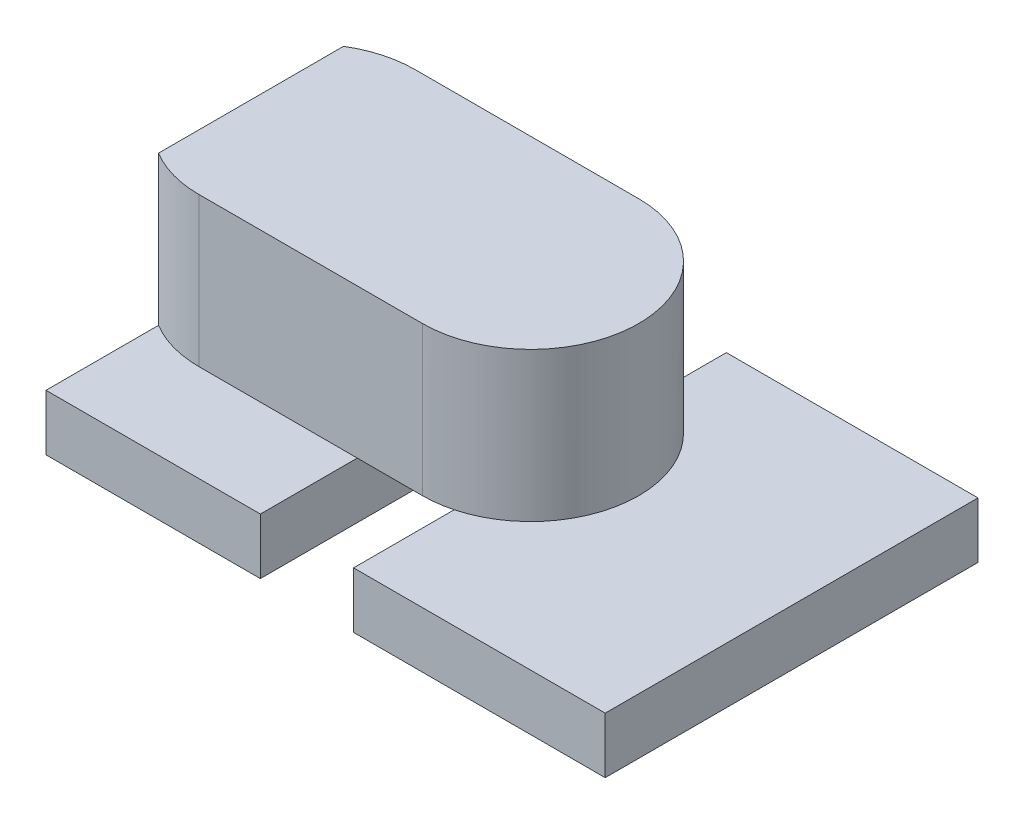
SolidWorks part; units mm, degrees
ref_plane "Front Plane" through (0, 0, 0) normal (0, 0, 1) x (1, 0, 0)
ref_plane "Top Plane" through (0, 0, 0) normal (0, 1, 0) x (1, 0, 0)
ref_plane "Right Plane" through (0, 0, 0) normal (1, 0, 0) x (0, 0, -1)
sketch "Sketch1" plane through (0, 0, 0) normal (0, 1, 0) x (1, 0, 0)
  line L1 (-7.5, -5) -> (7.5, -5)
  line L2 (-7.5, -5) -> (-7.5, 5)
  line L3 (-7.5, 5) -> (7.5, 5)
  line L4 (7.5, -5) -> (7.5, 5)
  line L5 (-7.5, -5) -> (7.5, 5) construction
  line L6 (-7.5, 5) -> (7.5, -5) construction
  point P0 (0, 0)
  dimension "D1" = 15
  dimension "D2" = 10
extrude "Boss-Extrude1" add sketch "Sketch1" along normal blind 1.5
sketch "Sketch2" plane through (0, 1.5, 0) normal (0, 1, 0) x (1, 0, 0)
  line L0 (-6, 0.5) -> (0, 0.5) construction
  line L1 (-6, 3.4) -> (0, 3.4)
  line L2 (-6, -2.4) -> (0, -2.4)
  line L3 (7.5, -5) -> (7.5, 5) construction
  line L4 (-7.5, 5) -> (-7.5, -5) construction
  line L5 (-7.5, 2.9819) -> (-7.5, -1.9819)
  arc A0 (-6, 3.4) -> (-7.5, 2.9819) centre (-6, 0.5) ccw
  arc A1 (0, -2.4) -> (0, 3.4) centre (0, 0.5) ccw
  arc A2 (-7.5, -1.9819) -> (-6, -2.4) centre (-6, 0.5) ccw
  point P3 (-3, 0.5)
  dimension "D4" = 2.9
  dimension "D1" = 7.5
  dimension "D2" = 6
  dimension "D3" = 0.5
extrude "Boss-Extrude2" add sketch "Sketch2" along normal blind 4
sketch "Sketch3" plane through (0, 0, 0) normal (0, -1, 0) x (1, 0, 0)
  line L0 (-7.5, 5) -> (7.5, 5) construction
  line L1 (0.75, -5) -> (-1.75, -5)
  line L2 (0.75, -5) -> (0.75, 5)
  line L3 (0.75, 5) -> (-1.75, 5)
  line L4 (-1.75, -5) -> (-1.75, 5)
  line L5 (0.75, -5) -> (-1.75, 5) construction
  line L6 (0.75, 5) -> (-1.75, -5) construction
  line L7 (7.5, -5) -> (-7.5, -5) construction
  line L9 (7.5, 5) -> (7.5, -5) construction
  point P0 (-0.5, 0)
  dimension "D1" = 2.5
  dimension "D2" = 8
extrude "Cut-Extrude1" cut sketch "Sketch3" against normal blind 1.5
